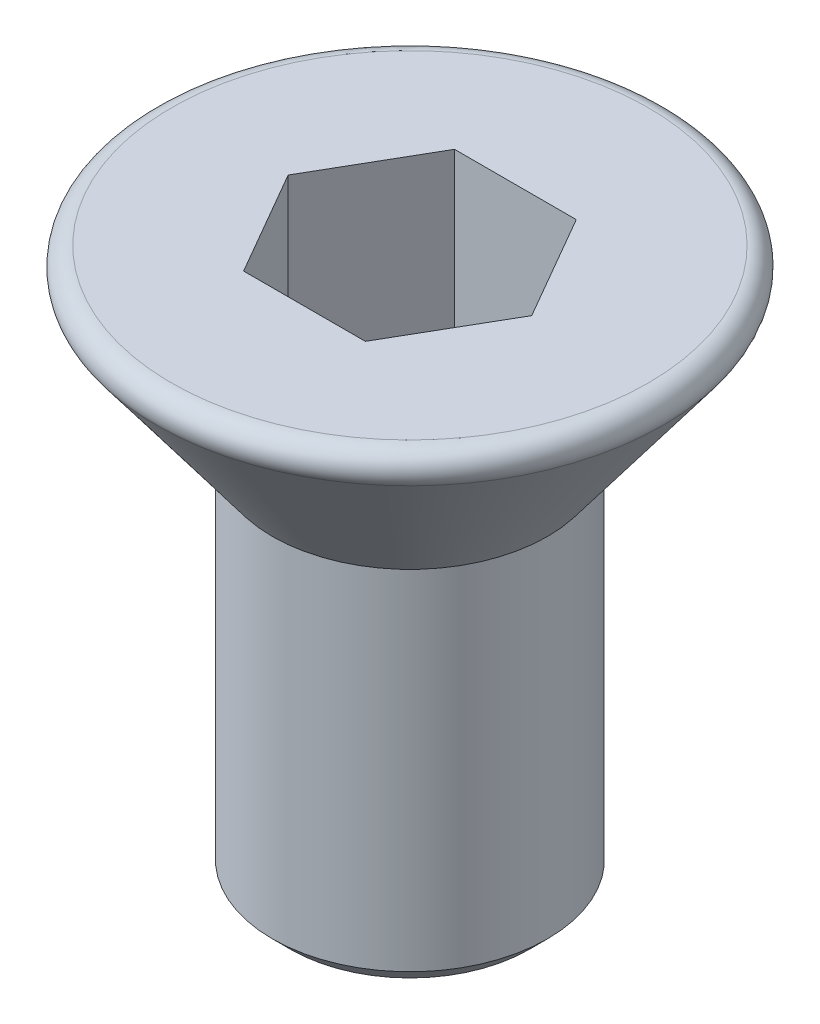
SolidWorks part; units mm, degrees
ref_plane "前视" through (0, 0, 0) normal (0, 0, 1) x (1, 0, 0)
ref_plane "上视" through (0, 0, 0) normal (0, 1, 0) x (1, 0, 0)
ref_plane "右视" through (0, 0, 0) normal (1, 0, 0) x (0, 0, -1)
sketch "草图1" plane through (0, 0, 0) normal (0, 0, 1) x (1, 0, 0)
  line L0 (0, 0) -> (0, -2)
  line L1 (0, -2) -> (1.5, -2)
  line L2 (3, 0) -> (0, 0)
  line L3 (1.5, -2) -> (3, 0)
  dimension "D1" = 3
  dimension "D2" = 1.5
  dimension "D3" = 2
revolve "旋转1" add sketch "草图1" angle 360 about L0
sketch "草图2" plane through (0, -2, 0) normal (0, -1, 0) x (1, 0, 0)
  circle A0 centre (0, 0) radius 1.5
extrude "凸台-拉伸1" add sketch "草图2" along normal blind 4
sketch "草图3" plane through (0, 0, 0) normal (0, 1, 0) x (1, 0, 0)
  line L1 (-1.3279, 0) -> (-0.664, -1.15)
  line L2 (-0.664, -1.15) -> (0.664, -1.15)
  line L3 (0.664, -1.15) -> (1.3279, 0)
  line L4 (1.3279, 0) -> (0.664, 1.15)
  line L5 (0.664, 1.15) -> (-0.664, 1.15)
  line L6 (-0.664, 1.15) -> (-1.3279, 0)
  circle A0 centre (0, 0) radius 1.15 construction
  dimension "D1" = 2.3
extrude "切除-拉伸1" cut sketch "草图3" against normal blind 2
chamfer "倒角1" distance 0.2 angle 45 1 edges at (1.5, -6, 0)
fillet "圆角1" radius 0.2 1 edges at (-3, 0, 0)
